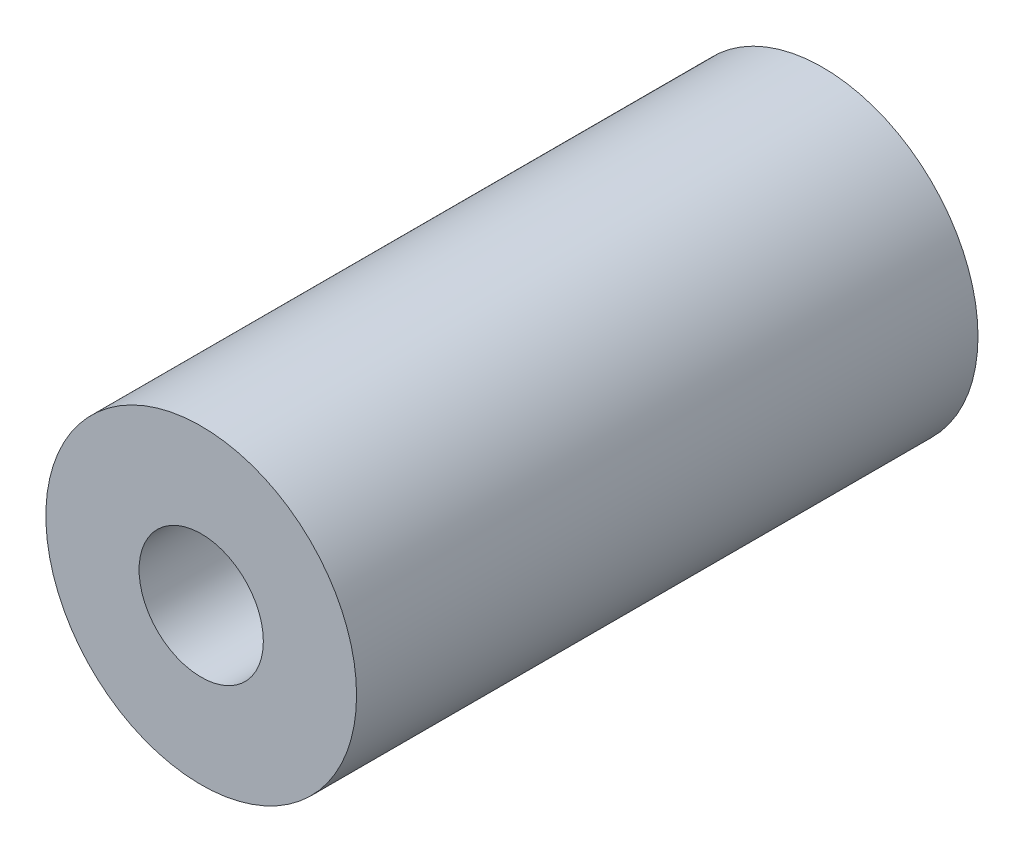
SolidWorks part; units mm, degrees
ref_plane "Front Plane" through (0, 0, 0) normal (0, 0, 1) x (1, 0, 0)
ref_plane "Top Plane" through (0, 0, 0) normal (0, 1, 0) x (1, 0, 0)
ref_plane "Right Plane" through (0, 0, 0) normal (1, 0, 0) x (0, 0, -1)
sketch "Sketch1" plane through (0, 0, 0) normal (0, 0, 1) x (1, 0, 0)
  circle A0 centre (0, 0) radius 7.9375
  circle A1 centre (0, 0) radius 3.175
  dimension "D1" = 6.35
  dimension "D2" = 15.875
extrude "Boss-Extrude1" add sketch "Sketch1" along normal blind 31.75 contours A0 A1
equation "\"Thick\"= \"in\""
